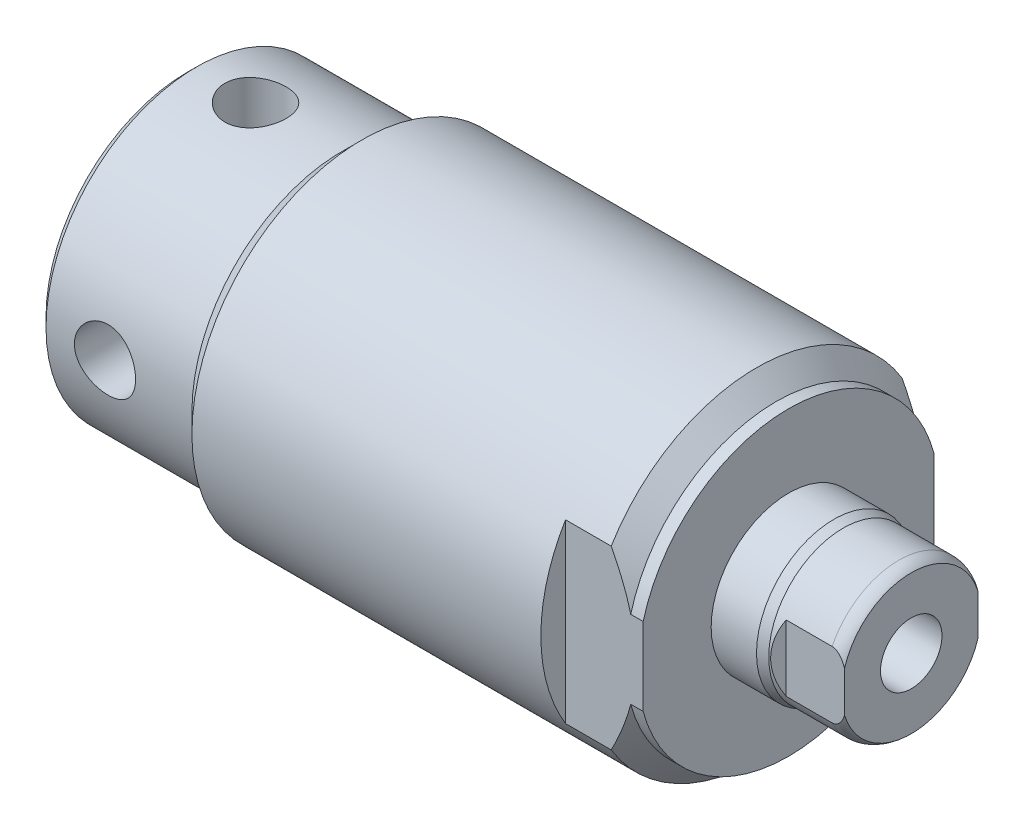
SolidWorks part; units mm, degrees
material "Alloy Steel"
ref_plane "Front Plane" through (0, 0, 0) normal (0, 0, 1) x (1, 0, 0)
ref_plane "Top Plane" through (0, 0, 0) normal (0, 1, 0) x (1, 0, 0)
ref_plane "Right Plane" through (0, 0, 0) normal (1, 0, 0) x (0, 0, -1)
ref_plane "Plane1" through (0, 0, 0) normal (0, 0, -1) x (-1, 0, 0)
sketch "Sketch1" plane through (0, 0, 0) normal (0, 0, -1) x (-1, 0, 0)
  line L0 (-59.2328, 5.7079) -> (-59.2328, 0)
  line L1 (-59.2328, 0) -> (0, 0)
  line L2 (0, 0) -> (0, 12.319)
  line L3 (0, 12.319) -> (-12.7, 12.319)
  line L4 (-14.3, 13.919) -> (-46.5838, 13.919)
  line L5 (-12.7, 12.319) -> (-14.3, 13.919)
  line L6 (-49.1998, 12.319) -> (-49.1998, 6.3373)
  line L7 (-53.6702, 6.096) -> (-58.2168, 6.096)
  line L8 (-59.2328, 0) -> (0, 0) construction
  line L9 (0, 0) -> (6.3339, 0) construction
  line L10 (-46.5838, 13.919) -> (-48.1838, 12.319)
  line L11 (-48.1838, 12.319) -> (-49.1998, 12.319)
  line L12 (-49.1998, 6.3373) -> (-52.9082, 6.3373)
  line L13 (-52.9082, 6.3373) -> (-53.6702, 6.096)
  arc A0 (-58.2168, 6.096) -> (-59.2328, 5.7079) centre (-58.2168, 4.572) ccw
  dimension "D6" = 1.524
  dimension "D1" = 27.838
  dimension "D2" = 24.638
  dimension "D3" = 45
  dimension "D4" = 12.192
  dimension "D5" = 1.016
  dimension "D7" = 10.033
  dimension "D8" = 49.1998
  dimension "D9" = 12.7
  dimension "D10" = 1.016
  dimension "D11" = 12.6746
  dimension "D12" = 0.762
  dimension "D13" = 5.5626
revolve "Revolve1" add sketch "Sketch1" angle 360 about L8
sketch "Sketch2" plane through (0, 0, 0) normal (0, 0, -1) x (-1, 0, 0)
  line L0 (-10.5664, 0) -> (-10.5664, 4.4196)
  line L1 (-10.5664, 4.4196) -> (-0.6604, 4.4196)
  line L2 (-0.6604, 4.4196) -> (-0.127, 4.953)
  line L3 (-0.127, 4.953) -> (0, 4.953)
  line L4 (0, -12.319) -> (0, 12.319) construction
  line L5 (0, 4.953) -> (0, 0)
  line L6 (-33.1433, 0) -> (0, 0) construction
  line L7 (0, 0) -> (-10.5664, 0)
  dimension "D1" = 9.906
  dimension "D2" = 10.5664
  dimension "D3" = 8.8392
  dimension "D4" = 45
  dimension "D5" = 0.127
revolve "Cut-Revolve1" cut sketch "Sketch2" angle 360 about L6
sketch "Sketch3" plane through (0, 0, 0) normal (0, 0, -1) x (-1, 0, 0)
  line L0 (-59.2328, 2.5146) -> (-59.2328, 0)
  line L1 (-59.2328, 0) -> (-48.0568, 0)
  line L2 (-48.0568, 0) -> (-49.5677, 2.5146)
  line L3 (-49.5677, 2.5146) -> (-59.2328, 2.5146)
  line L4 (-66.3139, 0) -> (-46.9899, 0) construction
  line L5 (-59.2328, 5.7079) -> (-59.2328, -5.7079) construction
  dimension "D1" = 5.0292
  dimension "D2" = 11.176
  dimension "D3" = 59
revolve "Cut-Revolve2" cut sketch "Sketch3" angle 360 about L4
chamfer "Chamfer1" distance 0.762 angle 45 1 edges at (0, 0, 12.319)
sketch "Sketch4" plane through (0, 0, 0) normal (0, 1, 0) x (1, 0, 0)
  line L0 (64.4289, 0) -> (49.673, 0) construction
  line L1 (53.8226, 6.096) -> (54.4576, 5.461)
  line L2 (54.4576, 5.461) -> (59.2328, 5.461)
  line L3 (59.2328, -5.7079) -> (59.2328, 5.7079) construction
  line L4 (59.2328, 5.461) -> (59.2328, 6.096)
  line L5 (59.2328, 6.096) -> (53.8226, 6.096)
  line L6 (58.2168, 6.096) -> (53.6702, 6.096) construction
  line L7 (59.2328, -6.096) -> (53.8226, -6.096)
  line L8 (59.2328, -5.461) -> (59.2328, -6.096)
  line L9 (54.4576, -5.461) -> (59.2328, -5.461)
  line L10 (53.8226, -6.096) -> (54.4576, -5.461)
  dimension "D1" = 45
  dimension "D2" = 10.922
  dimension "D3" = 4.7752
extrude "Cut-Extrude1" cut sketch "Sketch4" against normal through all and the other way through all
hole_wizard "Hole1" positions "3DSketch1" profile "Sketch5" legacy
sketch3d "3DSketch1"
  point P0 (5.588, 12.319, 0)
  dimension "D1" = 5.588
sketch "Sketch5" plane through (5.588, 12.319, 0) normal (1, 0, 0) x (0, 0, 1)
  line L0 (0, 0) -> (0, 4.064)
  line L1 (0, 4.064) -> (2.5019, 4.064)
  line L2 (2.5019, 4.064) -> (2.5019, 0)
  line L3 (2.5019, 0) -> (0, 0)
  line L4 (0, 110) -> (0, -10) construction
  dimension "Diameter" = 5.0038
  dimension "Depth" = 4.064
pattern_circular "CirPattern1" count 4 over 360 about axis through (0, 0, 0) along (1, 0, 0) of "Hole1"
sketch "Sketch6" plane through (0, 0, 0) normal (0, 1, 0) x (1, 0, 0)
  line L0 (49.1998, -12.319) -> (49.1998, 12.319) construction
  line L1 (49.1998, 11.9) -> (42.8498, 11.9)
  line L2 (49.1998, 11.9) -> (49.1998, 13.919)
  line L3 (49.1998, 13.919) -> (42.8498, 13.919)
  line L4 (42.8498, 11.9) -> (42.8498, 13.919)
  line L5 (46.5838, 13.919) -> (14.3, 13.919) construction
  line L6 (14.3, -13.919) -> (46.5838, -13.919) construction
  line L7 (49.1998, -11.9) -> (42.8498, -11.9)
  line L8 (49.1998, -11.9) -> (49.1998, -13.919)
  line L9 (49.1998, -13.919) -> (42.8498, -13.919)
  line L10 (42.8498, -11.9) -> (42.8498, -13.919)
  dimension "D1" = 6.35
  dimension "D2" = 23.8
extrude "Cut-Extrude2" cut sketch "Sketch6" against normal through all and the other way through all
